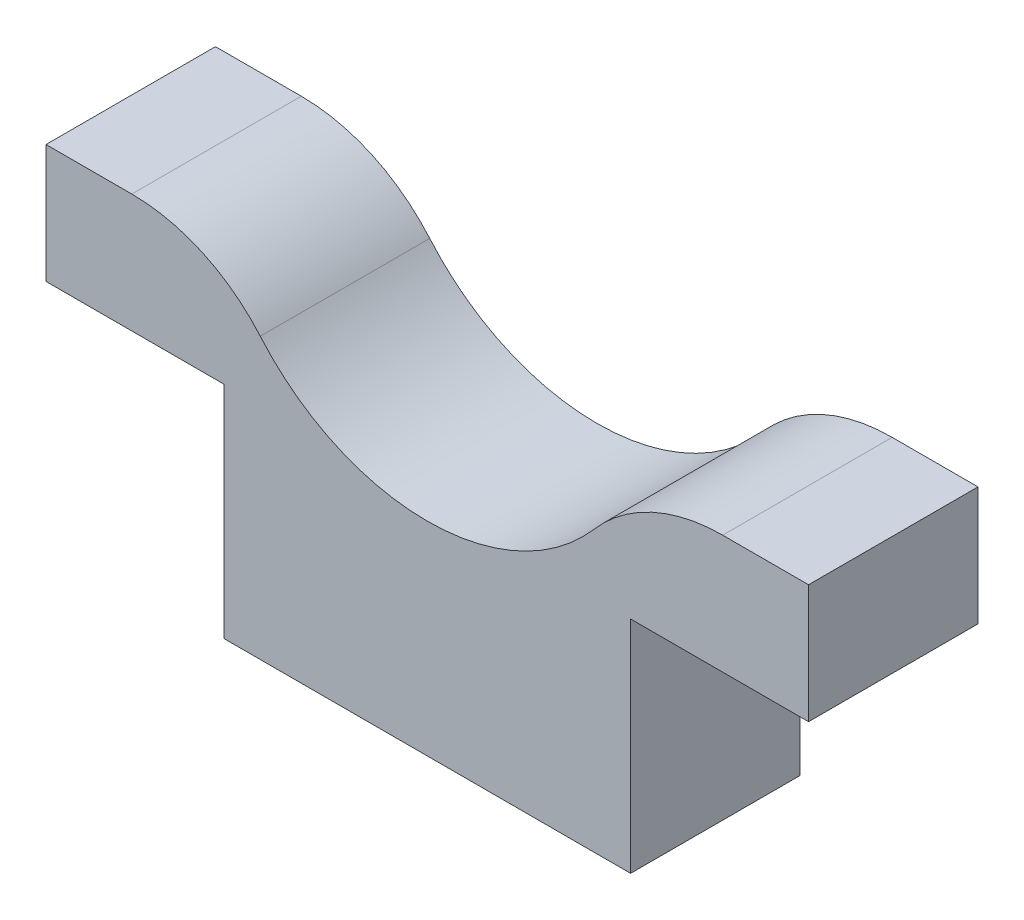
SolidWorks part; units mm, degrees
material "ABS"
ref_plane "Front Plane" through (0, 0, 0) normal (0, 0, 1) x (1, 0, 0)
ref_plane "Top Plane" through (0, 0, 0) normal (0, 1, 0) x (1, 0, 0)
ref_plane "Right Plane" through (0, 0, 0) normal (1, 0, 0) x (0, 0, -1)
sketch "Sketch1" plane through (0, 0, 0) normal (0, 0, 1) x (1, 0, 0)
  line L0 (24, 13) -> (34.5, 13)
  line L1 (0, 0) -> (24, 0)
  line L2 (0, 0) -> (0, 13)
  line L3 (0, 13) -> (24, 13)
  line L4 (24, 0) -> (24, 13)
  line L5 (0, 13) -> (-10.5, 13)
  line L6 (-10.5, 13) -> (-10.5, 20)
  line L7 (-10.5, 20) -> (34.5, 20)
  line L8 (34.5, 13) -> (34.5, 20)
  dimension "D1" = 13
  dimension "D2" = 7
  dimension "D3" = 45
  dimension "D4" = 24
extrude "Boss-Extrude1" add sketch "Sketch1" along normal blind 10 contours L1 L4 L3 L2 | L0 L8 L7 L6 L5 L3
sketch "Sketch2" plane through (0, 0, 0) normal (0, 0, -1) x (-1, 0, 0)
  line L0 (10.5, 20) -> (-34.5, 20) construction
  line L1 (-12, 20) -> (-12, 0) construction
  line L2 (0, 20) -> (-24, 20)
  line L3 (0, 0) -> (-24, 0) construction
  line L4 (10.5, 20) -> (-34.5, 20) construction
  arc A0 (0, 20) -> (-24, 20) centre (-12, 25) cw
  point P11 (-12, 20)
  point P12 (-20.8037, 20)
  point P15 (0, 0)
  point P16 (0, 0)
  point P18 (0, 20)
  point P19 (-12, 24.9425)
  dimension "D1" = 13
extrude "Cut-Extrude2" cut sketch "Sketch2" against normal through all
fillet "Fillet1" radius 10 2 edges at (0, 20, 5) (24, 20, 5)
